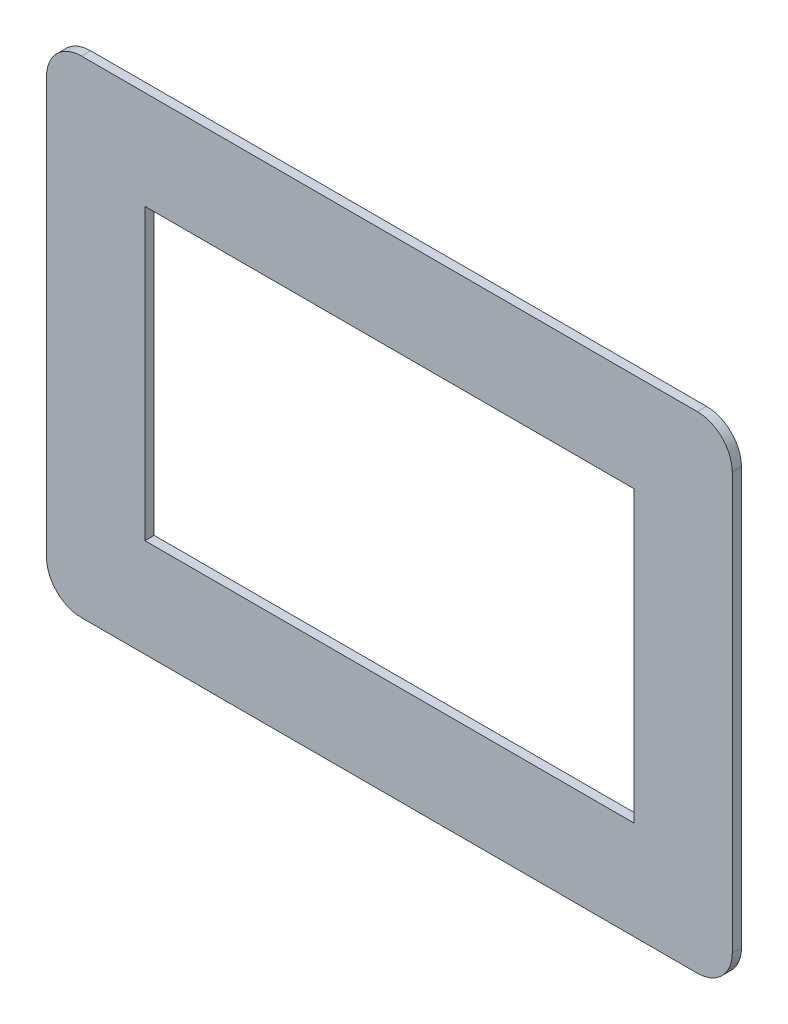
SolidWorks part; units mm, degrees
ref_plane "Front Plane" through (0, 0, 0) normal (0, 0, 1) x (1, 0, 0)
ref_plane "Top Plane" through (0, 0, 0) normal (0, 1, 0) x (1, 0, 0)
ref_plane "Right Plane" through (0, 0, 0) normal (1, 0, 0) x (0, 0, -1)
sketch "Sketch1" plane through (0, 0, 0) normal (0, 0, 1) x (1, 0, 0)
  line L1 (79.8762, 45.6) -> (-74.1238, 45.6)
  line L2 (79.8762, 45.6) -> (79.8763, -45.6)
  line L3 (79.8763, -45.6) -> (-74.1238, -45.6)
  line L4 (-74.1238, 45.6) -> (-74.1238, -45.6)
  line L5 (99.8763, 73.6) -> (-94.1237, 73.6) construction
  line L6 (107.8762, 65.6) -> (107.8762, -65.6) construction
  line L7 (99.8763, -73.6) -> (-94.1237, -73.6) construction
  line L8 (-102.1237, 65.6) -> (-102.1237, -65.6) construction
  line L9 (-22.7251, 0) -> (22.7251, 0) construction
  line L10 (99.8763, 76.6) -> (-94.1237, 76.6)
  line L11 (-105.1237, 65.6) -> (-105.1237, -65.6)
  line L12 (99.8763, -76.6) -> (-94.1237, -76.6)
  line L13 (110.8762, 65.6) -> (110.8763, -65.6)
  line L14 (2.8762, 175.6385) -> (2.8763, -176.0421) construction
  arc A0 (-94.1237, 73.6) -> (-102.1237, 65.6) centre (-94.1237, 65.6) ccw construction
  arc A1 (-94.1237, -73.6) -> (-102.1237, -65.6) centre (-94.1237, -65.6) cw construction
  arc A2 (99.8763, 73.6) -> (107.8762, 65.6) centre (99.8763, 65.6) cw construction
  arc A3 (107.8762, -65.6) -> (99.8763, -73.6) centre (99.8763, -65.6) cw construction
  arc A4 (-94.1237, 76.6) -> (-105.1237, 65.6) centre (-94.1237, 65.6) ccw
  arc A5 (-94.1237, -76.6) -> (-105.1237, -65.6) centre (-94.1237, -65.6) cw
  arc A6 (110.8763, -65.6) -> (99.8763, -76.6) centre (99.8763, -65.6) cw
  arc A7 (99.8763, 76.6) -> (110.8762, 65.6) centre (99.8763, 65.6) cw
  point P10 (107.8763, 0)
  point P13 (81.2469, 71.23)
  point P14 (-83.7531, 71.23)
  point P39 (2.8763, -76.6)
  dimension "D5" = 8
  dimension "D6" = 8
  dimension "D1" = 28
  dimension "D2" = 28
  dimension "D3" = 28
  dimension "D4" = 2.37
  dimension "D7" = 3
extrude "Boss-Extrude1" add sketch "Sketch1" along normal blind 2.9
sketch "Sketch2" plane through (0, 0, 0) normal (0, 0, 1) x (1, 0, 0)
  line L8 (99.8763, 75.6) -> (-94.1237, 75.6)
  line L9 (-104.1237, 65.6) -> (-104.1237, -65.6)
  line L10 (-94.1237, -75.6) -> (99.8763, -75.6)
  line L11 (109.8763, -65.6) -> (109.8763, 65.6)
  line L12 (99.8763, 75.6) -> (-94.1237, 75.6)
  line L13 (-104.1237, 65.6) -> (-104.1237, -65.6)
  line L14 (-94.1237, -75.6) -> (99.8763, -75.6)
  line L15 (109.8763, -65.6) -> (109.8763, 65.6)
  line L18 (99.8763, 73.6) -> (-94.1237, 73.6)
  line L19 (-102.1237, 65.6) -> (-102.1237, -65.6)
  line L20 (-94.1237, -73.6) -> (99.8763, -73.6)
  line L21 (107.8763, -65.6) -> (107.8763, 65.6)
  line L22 (99.8763, 73.6) -> (-94.1237, 73.6)
  line L23 (-102.1237, 65.6) -> (-102.1237, -65.6)
  line L24 (-94.1237, -73.6) -> (99.8763, -73.6)
  line L25 (107.8763, -65.6) -> (107.8763, 65.6)
  arc A8 (109.8763, 65.6) -> (99.8763, 75.6) centre (99.8763, 65.6) ccw
  arc A9 (-94.1237, 75.6) -> (-104.1237, 65.6) centre (-94.1237, 65.6) ccw
  arc A10 (-104.1237, -65.6) -> (-94.1237, -75.6) centre (-94.1237, -65.6) ccw
  arc A11 (99.8763, -75.6) -> (109.8763, -65.6) centre (99.8763, -65.6) ccw
  arc A12 (109.8763, 65.6) -> (99.8763, 75.6) centre (99.8763, 65.6) ccw
  arc A13 (-94.1237, 75.6) -> (-104.1237, 65.6) centre (-94.1237, 65.6) ccw
  arc A14 (-104.1237, -65.6) -> (-94.1237, -75.6) centre (-94.1237, -65.6) ccw
  arc A15 (99.8763, -75.6) -> (109.8763, -65.6) centre (99.8763, -65.6) ccw
  arc A17 (107.8763, 65.6) -> (99.8763, 73.6) centre (99.8763, 65.6) ccw
  arc A18 (-94.1237, 73.6) -> (-102.1237, 65.6) centre (-94.1237, 65.6) ccw
  arc A19 (-102.1237, -65.6) -> (-94.1237, -73.6) centre (-94.1237, -65.6) ccw
  arc A20 (99.8763, -73.6) -> (107.8763, -65.6) centre (99.8763, -65.6) ccw
  arc A21 (107.8763, 65.6) -> (99.8763, 73.6) centre (99.8763, 65.6) ccw
  arc A22 (-94.1237, 73.6) -> (-102.1237, 65.6) centre (-94.1237, 65.6) ccw
  arc A23 (-102.1237, -65.6) -> (-94.1237, -73.6) centre (-94.1237, -65.6) ccw
  arc A24 (99.8763, -73.6) -> (107.8763, -65.6) centre (99.8763, -65.6) ccw
  dimension "D1" = 1
  dimension "D2" = 3
extrude "Cut-Extrude3" cut sketch "Sketch2" along normal blind 1.5
